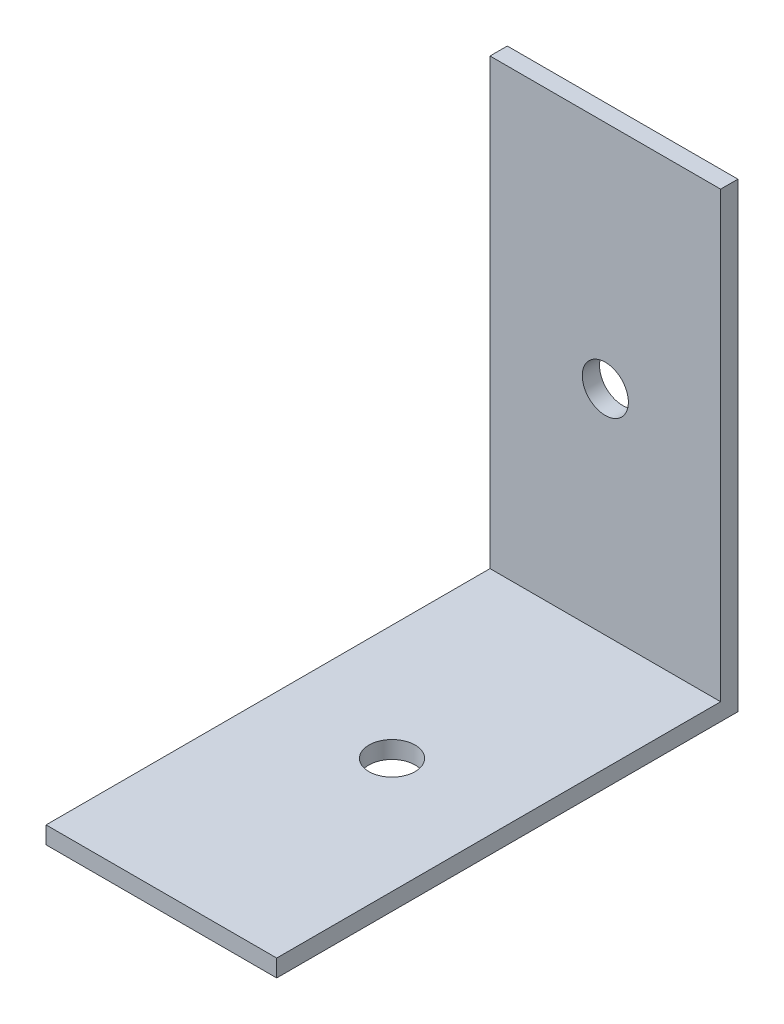
SolidWorks part; units mm, degrees
ref_plane "Front Plane" through (0, 0, 0) normal (0, 0, 1) x (1, 0, 0)
ref_plane "Top Plane" through (0, 0, 0) normal (0, 1, 0) x (1, 0, 0)
ref_plane "Right Plane" through (0, 0, 0) normal (1, 0, 0) x (0, 0, -1)
sketch "Sketch1" plane through (0, 0, 0) normal (0, 1, 0) x (1, 0, 0)
  line L0 (0, 20) -> (0, 0) construction
  line L1 (-10, 20) -> (10, 20)
  line L2 (-10, 20) -> (-10, -20)
  line L3 (-10, -20) -> (10, -20)
  line L4 (10, 20) -> (10, -20)
  line L5 (-10, 20) -> (10, -20) construction
  line L6 (-10, -20) -> (10, 20) construction
  circle A0 centre (0, 0) radius 2
  point P0 (0, 0)
  dimension "D4" = 4
  dimension "D1" = 20
  dimension "D2" = 40
  dimension "D3" = 20
extrude "Boss-Extrude1" add sketch "Sketch1" along normal blind 1.5
sketch "Sketch2" plane through (0, 1.5, 0) normal (0, 1, 0) x (1, 0, 0)
  line L0 (-10, 20) -> (10, 20)
  line L1 (-10, 20) -> (-10, 18.5)
  line L2 (10, 20) -> (10, 18.5)
  line L3 (-10, 18.5) -> (10, 18.5)
  dimension "D1" = 1.5
extrude "Boss-Extrude2" add sketch "Sketch2" along normal blind 38.5 contours L3 L2 L0 L1
sketch "Sketch3" plane through (0, 0, -20) normal (0, 0, -1) x (-1, 0, 0)
  line L0 (0, 0) -> (0, 20) construction
  circle A0 centre (0, 20) radius 2
  dimension "D2" = 4
  dimension "D1" = 20
extrude "Cut-Extrude1" cut sketch "Sketch3" against normal up to surface (1.5 mm away) contours A0 up to face at (0, 20.75, -18.5)
